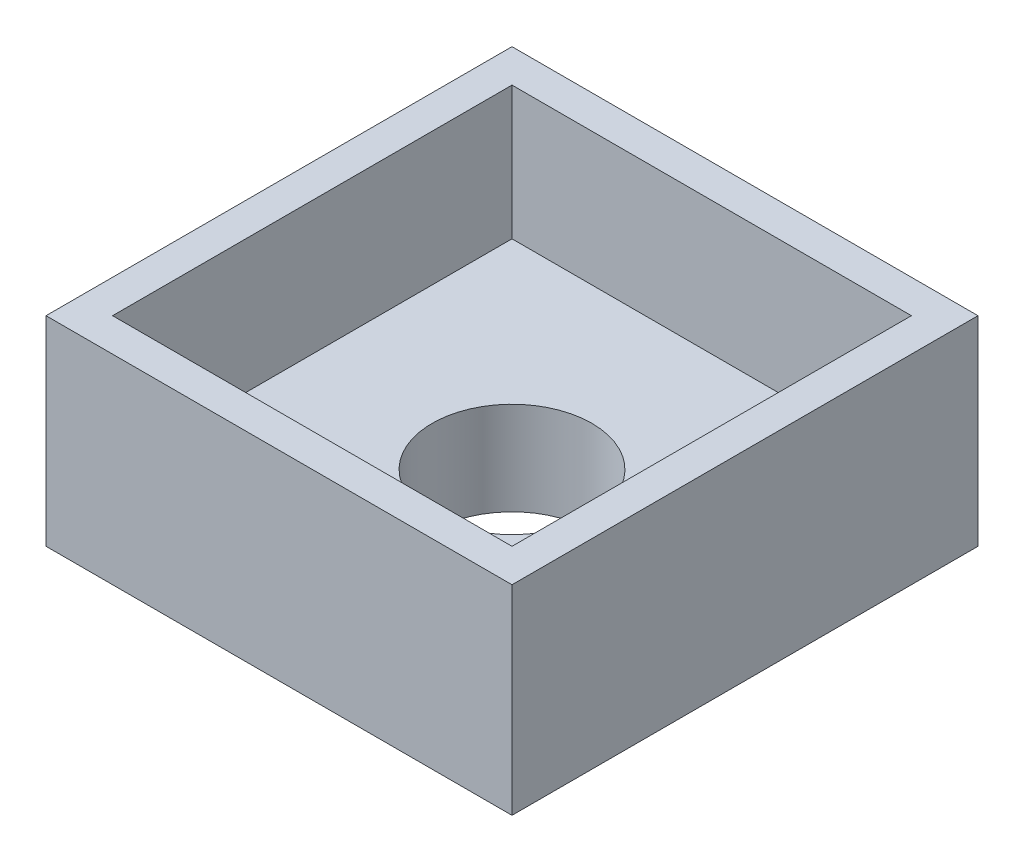
SolidWorks part; units mm, degrees
ref_plane "Front Plane" through (0, 0, 0) normal (0, 0, 1) x (1, 0, 0)
ref_plane "Top Plane" through (0, 0, 0) normal (0, 1, 0) x (1, 0, 0)
ref_plane "Right Plane" through (0, 0, 0) normal (1, 0, 0) x (0, 0, -1)
sketch "Sketch1" plane through (0, 0, 0) normal (0, 1, 0) x (1, 0, 0)
  line L1 (-15, -15) -> (15, -15)
  line L2 (-15, -15) -> (-15, 15)
  line L3 (-15, 15) -> (15, 15)
  line L4 (15, -15) -> (15, 15)
  line L5 (-15, -15) -> (15, 15) construction
  line L6 (-15, 15) -> (15, -15) construction
  line L7 (-17.5, -17.5) -> (17.5, -17.5)
  line L8 (-17.5, -17.5) -> (-17.5, 17.5)
  line L9 (-17.5, 17.5) -> (17.5, 17.5)
  line L10 (17.5, -17.5) -> (17.5, 17.5)
  line L11 (-17.5, -17.5) -> (17.5, 17.5) construction
  line L12 (-17.5, 17.5) -> (17.5, -17.5) construction
  point P0 (0, 0)
  point P6 (0, 0)
  dimension "D1" = 30
  dimension "D2" = 30
  dimension "D3" = 35
  dimension "D4" = 35
extrude "Boss-Extrude1" add sketch "Sketch1" along normal blind 10
sketch "Sketch4" plane through (0, 0, 0) normal (0, -1, 0) x (1, 0, 0)
  line L0 (17.5, 17.5) -> (17.5, -17.5) construction
  line L1 (-17.5, -17.5) -> (17.5, -17.5)
  line L2 (-17.5, -17.5) -> (-17.5, 17.5)
  line L3 (-17.5, 17.5) -> (17.5, 17.5)
  line L4 (17.5, -17.5) -> (17.5, 17.5)
  line L5 (-17.5, -17.5) -> (17.5, 17.5) construction
  line L6 (-17.5, 17.5) -> (17.5, -17.5) construction
  line L7 (-17.5, 17.5) -> (17.5, 17.5) construction
  point P0 (0, 0)
  dimension "D1" = 0
extrude "Boss-Extrude2" add sketch "Sketch4" along normal blind 5
sketch "Sketch5" plane through (0, -5, 0) normal (0, -1, 0) x (1, 0, 0)
  circle A0 centre (0, 0) radius 6
  dimension "D1" = 12
extrude "Cut-Extrude1" cut sketch "Sketch5" against normal through all
sketch "Sketch6" plane through (0, -5, 0) normal (0, -1, 0) x (-1, 0, 0)
  circle A0 centre (0, 0) radius 7
  circle A1 centre (0, 0) radius 6
  dimension "D1" = 14
extrude "Boss-Extrude3" add sketch "Sketch6" along normal blind 2
